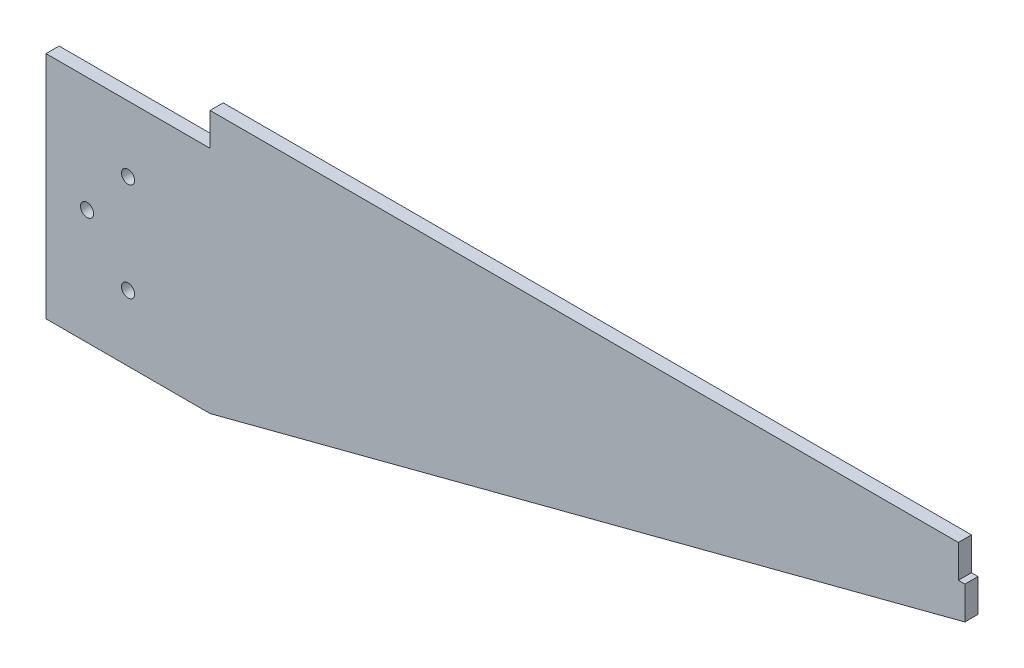
SolidWorks part; units mm, degrees
ref_plane "Front Plane" through (0, 0, 0) normal (0, 0, 1) x (1, 0, 0)
ref_plane "Top Plane" through (0, 0, 0) normal (0, 1, 0) x (1, 0, 0)
ref_plane "Right Plane" through (0, 0, 0) normal (1, 0, 0) x (0, 0, -1)
sketch "Sketch1" plane through (0, 0, 0) normal (0, 0, 1) x (1, 0, 0)
  line L0 (128, 30.093) -> (128, 40.093)
  line L1 (128, 40.093) -> (-100, 40.093)
  line L2 (-100, 40.093) -> (-100, 20.093)
  line L3 (-100, 20.093) -> (-130, 20.093)
  line L4 (-130, 20.093) -> (-130, -39.907)
  line L5 (-130, -39.907) -> (-100, -39.907)
  line L6 (-100, -39.907) -> (130, 20.093)
  line L7 (130, 20.093) -> (130, 30.093)
  line L8 (130, 30.093) -> (128, 30.093)
  dimension "D1" = 228
  dimension "D2" = 60
extrude "Boss-Extrude1" add sketch "Sketch1" along normal blind 4
sketch "Sketch2" plane through (0, 0, 4) normal (0, 0, 1) x (1, 0, 0)
  line L0 (-150, 30.093) -> (-150, -39.907)
  line L1 (-150, -39.907) -> (-130, -39.907)
  line L4 (-150, -869.907) -> (-100, -869.907)
  line L5 (-100, -869.907) -> (-100, 30.093)
  line L6 (-100, 30.093) -> (-150, 30.093)
  line L7 (-150, 30.093) -> (-150, -869.907)
  line L8 (-150, -869.907) -> (-100, -869.907)
  line L9 (-100, 20.093) -> (-100, 30.093)
  line L10 (-100, 30.093) -> (-150, 30.093)
  line L17 (128, 30.093) -> (128, 40.093)
  line L18 (128, 40.093) -> (-100, 40.093)
  line L19 (-100, 40.093) -> (-100, 20.093)
  line L20 (-100, 20.093) -> (-130, 20.093)
  line L21 (-130, 20.093) -> (-130, -39.907)
  line L22 (-130, -39.907) -> (-100, -39.907)
  line L23 (-100, -39.907) -> (130, 20.093)
  line L24 (130, 20.093) -> (130, 30.093)
  line L25 (130, 30.093) -> (128, 30.093)
  line L26 (128, 30.093) -> (128, 40.093)
  line L28 (-100, 30.093) -> (-100, 20.093)
  line L29 (-100, 20.093) -> (-130, 20.093)
  line L30 (-130, 20.093) -> (-130, -39.907)
  line L33 (130, 20.093) -> (130, 30.093)
  line L34 (130, 30.093) -> (128, 30.093)
  line M17 (-100, 40.093) -> (-100, 20.093)
  line M18 (-100, 20.093) -> (-130, 20.093)
  line M19 (-130, 20.093) -> (-130, -39.907)
  dimension "D1" = 0
  dimension "D2" = 0
extrude "Boss-Extrude2" add sketch "Sketch2" against normal up to surface (4 mm away) contours L10 L0 L1 M17 M19 M18 up to face at (-4.8889, 13.4263, 0)
sketch "Sketch3" plane through (0, 0, 4) normal (0, 0, 1) x (1, 0, 0)
  line L0 (-150, 30.093) -> (-150, -39.907) construction
  line L1 (-150, 30.093) -> (-100, 30.093) construction
  line L2 (-125, 30.093) -> (-125, -39.907) construction
  line L3 (-150, -39.907) -> (-100, -39.907) construction
  line L4 (-150, -4.907) -> (-125, -4.907) construction
  circle A0 centre (-125, 10.093) radius 2
  circle A2 centre (-125, -19.907) radius 2
  circle A3 centre (-137.5, -4.907) radius 2
  dimension "D1" = 4
  dimension "D2" = 20
  dimension "D3" = 20
extrude "Cut-Extrude1" cut sketch "Sketch3" against normal up to next
